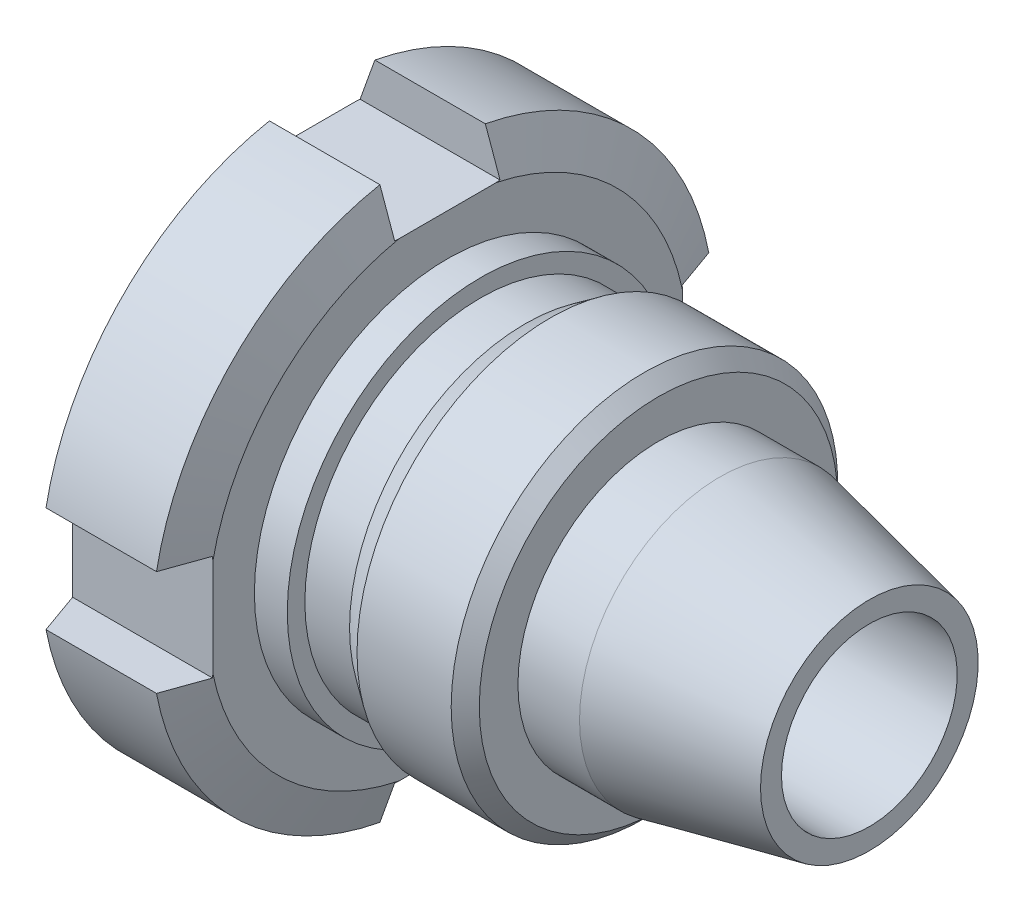
SolidWorks part; units mm, degrees
material "6061-T6 (SS)"
ref_plane "Front Plane" through (0, 0, 0) normal (0, 0, 1) x (1, 0, 0)
ref_plane "Top Plane" through (0, 0, 0) normal (0, 1, 0) x (1, 0, 0)
ref_plane "Right Plane" through (0, 0, 0) normal (1, 0, 0) x (0, 0, -1)
sketch "Sketch1" plane through (0, 0, 0) normal (0, 0, 1) x (1, 0, 0)
  line L0 (0, 6.35) -> (0, 21.6662)
  line L1 (1.359, 25.4) -> (11.341, 25.4)
  line L2 (12.7, 21.6662) -> (12.7, 17.4625)
  line L3 (12.7, 17.4625) -> (15.6718, 17.4625)
  line L4 (15.6718, 17.4625) -> (15.6718, 15.875)
  line L5 (15.6718, 15.875) -> (19.7104, 15.875)
  line L6 (19.7104, 15.875) -> (21.971, 17.4625)
  line L7 (21.971, 17.4625) -> (30.48, 17.4625)
  line L8 (31.75, 16.1925) -> (31.75, 12.7)
  line L9 (31.75, 12.7) -> (37.3126, 12.7)
  line L10 (37.3126, 12.7) -> (50.8, 9.8332)
  line L11 (50.8, 9.8332) -> (50.8, 7.9375)
  line L12 (50.8, 7.9375) -> (38.1, 7.9375)
  line L14 (37.1461, 6.35) -> (0, 6.35)
  line L15 (0, 0) -> (50.8, 0) construction
  line L16 (0, 21.6662) -> (1.359, 25.4)
  line L17 (12.7, 21.6662) -> (11.341, 25.4)
  line L18 (38.1, 7.9375) -> (37.1461, 6.35)
  line L19 (30.48, 17.4625) -> (31.75, 16.1925)
  point P10 (31.75, 17.4625)
  dimension "D1" = 50.8
  dimension "D3" = 12
  dimension "D4" = 25.4
  dimension "D5" = 6.35
  dimension "D6" = 7.9375
  dimension "D7" = 13.4874
  dimension "D8" = 19.05
  dimension "D9" = 28.829
  dimension "D10" = 31.0896
  dimension "D11" = 35.1282
  dimension "D12" = 38.1
  dimension "D13" = 17.4625
  dimension "D14" = 15.875
  dimension "D15" = 12.7
  dimension "D16" = 3.7338
  dimension "D17" = 20
  dimension "D18" = 20
  dimension "D19" = 3.7338
  dimension "D20" = 59
  dimension "D21" = 12.7
revolve "Revolve1" add sketch "Sketch1" angle 360 about L15
sketch "Sketch2" plane through (0, 0, 0) normal (-1, 0, 0) x (0, 0, 1)
  line L0 (0, 0) -> (0, 25.4) construction
  line L1 (-4.7625, 21.2157) -> (-4.7625, 24.9495)
  line L2 (4.7625, 21.2157) -> (4.7625, 24.9495)
  line L3 (-4.7625, 21.2157) -> (4.7625, 21.2157)
  circle A0 centre (0, 0) radius 25.4 construction
  arc A1 (4.7625, 24.9495) -> (-4.7625, 24.9495) centre (0, 0) ccw
  point P8 (4.7625, 24.9495)
  point P9 (-4.7625, 24.9495)
  dimension "D1" = 9.525
  dimension "D2" = 4.7625
  dimension "D3" = 3.7338
extrude "Cut-Extrude1" cut sketch "Sketch2" against normal up to next
pattern_circular "CirPattern1" count 4 over 360 about axis through (0, 0, 0) along (1, 0, 0) of "Cut-Extrude1"
